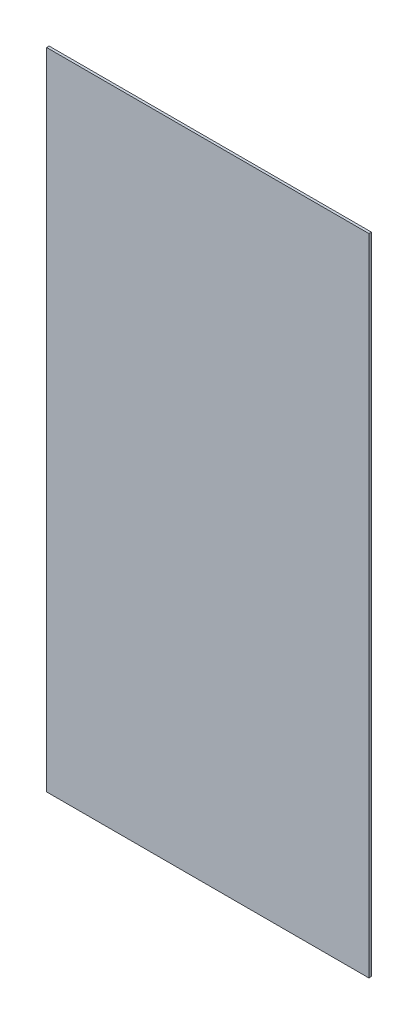
SolidWorks part; units mm, degrees
ref_plane "Спереди" through (0, 0, 0) normal (0, 0, 1) x (1, 0, 0)
ref_plane "Сверху" through (0, 0, 0) normal (0, 1, 0) x (1, 0, 0)
ref_plane "Справа" through (0, 0, 0) normal (1, 0, 0) x (0, 0, -1)
sketch "Эскиз1" plane through (0, 0, 0) normal (0, 0, 1) x (1, 0, 0)
  line L0 (25.4, 25.4) -> (75.4, 25.4)
  line L1 (75.4, 25.4) -> (75.4, 125.4)
  line L2 (75.4, 125.4) -> (25.4, 125.4)
  line L3 (25.4, 125.4) -> (25.4, 25.4)
  point P4 (125.4, 25.4)
extrude "Board" add sketch "Эскиз1" along normal blind 0.3912
